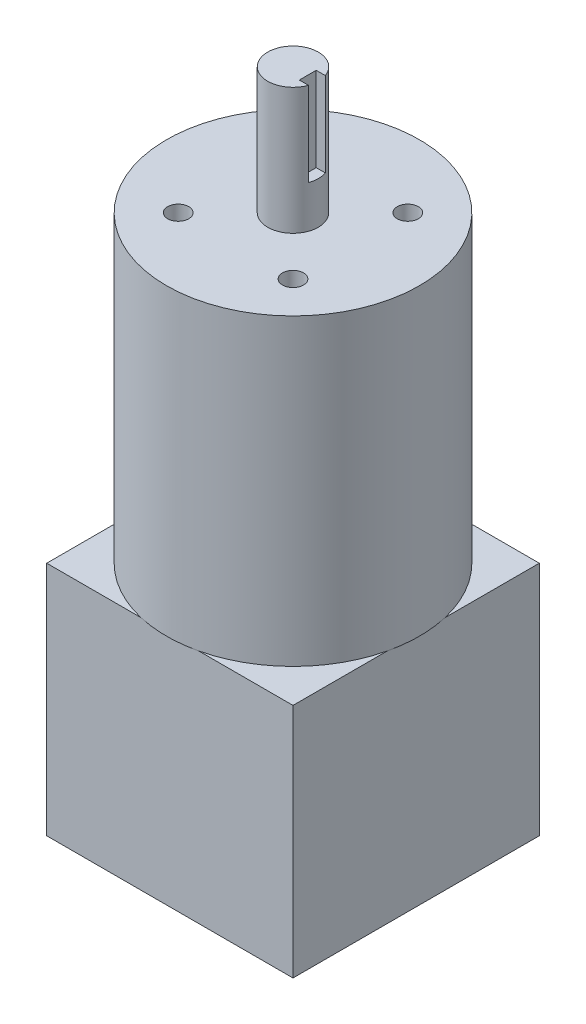
SolidWorks part; units mm, degrees
ref_plane "Front Plane" through (0, 0, 0) normal (0, 0, 1) x (1, 0, 0)
ref_plane "Top Plane" through (0, 0, 0) normal (0, 1, 0) x (1, 0, 0)
ref_plane "Right Plane" through (0, 0, 0) normal (1, 0, 0) x (0, 0, -1)
sketch "Sketch1" plane through (0, 0, 0) normal (0, 1, 0) x (1, 0, 0)
  line L1 (-29.21, -29.21) -> (29.21, -29.21)
  line L2 (-29.21, -29.21) -> (-29.21, 29.21)
  line L3 (-29.21, 29.21) -> (29.21, 29.21)
  line L4 (29.21, -29.21) -> (29.21, 29.21)
  line L5 (-29.21, -29.21) -> (29.21, 29.21) construction
  line L6 (-29.21, 29.21) -> (29.21, -29.21) construction
  point P0 (0, 0)
  dimension "D1" = 58.42
  dimension "D2" = 58.42
extrude "Boss-Extrude1" add sketch "Sketch1" along normal blind 56
sketch "Sketch2" plane through (0, 56, 0) normal (0, 1, 0) x (1, 0, 0)
  circle A0 centre (0, 0) radius 30
  dimension "D1" = 60
extrude "Boss-Extrude2" add sketch "Sketch2" along normal blind 72
sketch "Sketch3" plane through (0, 128, 0) normal (0, 1, 0) x (1, 0, 0)
  circle A0 centre (0, 0) radius 6
  dimension "D1" = 12
extrude "Boss-Extrude3" add sketch "Sketch3" along normal blind 30
sketch "Sketch4" plane through (0, 128, 0) normal (0, 1, 0) x (1, 0, 0)
  line L0 (0, 0) -> (0, 40.4963) construction
  line L1 (0, 0) -> (-37.1126, 37.1126) construction
  line L2 (0, 0) -> (40.6269, 0) construction
  circle A0 centre (0, 0) radius 16 construction
  circle A1 centre (0, 0) radius 22.5 construction
  circle A2 centre (-13.6118, 13.6118) radius 2.5
  circle A3 centre (0, 0) radius 19.25 construction
  circle A4 centre (13.6118, 13.6118) radius 2.5
  circle A5 centre (13.6118, -13.6118) radius 2.5
  circle A6 centre (-13.6118, -13.6118) radius 2.5
  dimension "D1" = 32
  dimension "D2" = 45
  dimension "D3" = 5
  dimension "D5" = 38.5
  dimension "D4" = 45
extrude "Cut-Extrude1" cut sketch "Sketch4" against normal blind 25.4
sketch "Sketch5" plane through (0, 158, 0) normal (0, 1, 0) x (1, 0, 0)
  line L1 (6, 2) -> (3.5, 2)
  line L2 (6, 2) -> (6, -2)
  line L3 (6, -2) -> (3.5, -2)
  line L4 (3.5, 2) -> (3.5, -2)
  line L5 (6, 2) -> (3.5, -2) construction
  line L6 (6, -2) -> (3.5, 2) construction
  circle A1 centre (0, 0) radius 6 construction
  circle A2 centre (0, 0) radius 6 construction
  point P0 (4.75, 0)
  point P5 (-6, 0)
  dimension "D1" = 4
  dimension "D2" = 2.5
  dimension "D3" = 9.5
extrude "Cut-Extrude2" cut sketch "Sketch5" against normal blind 20
